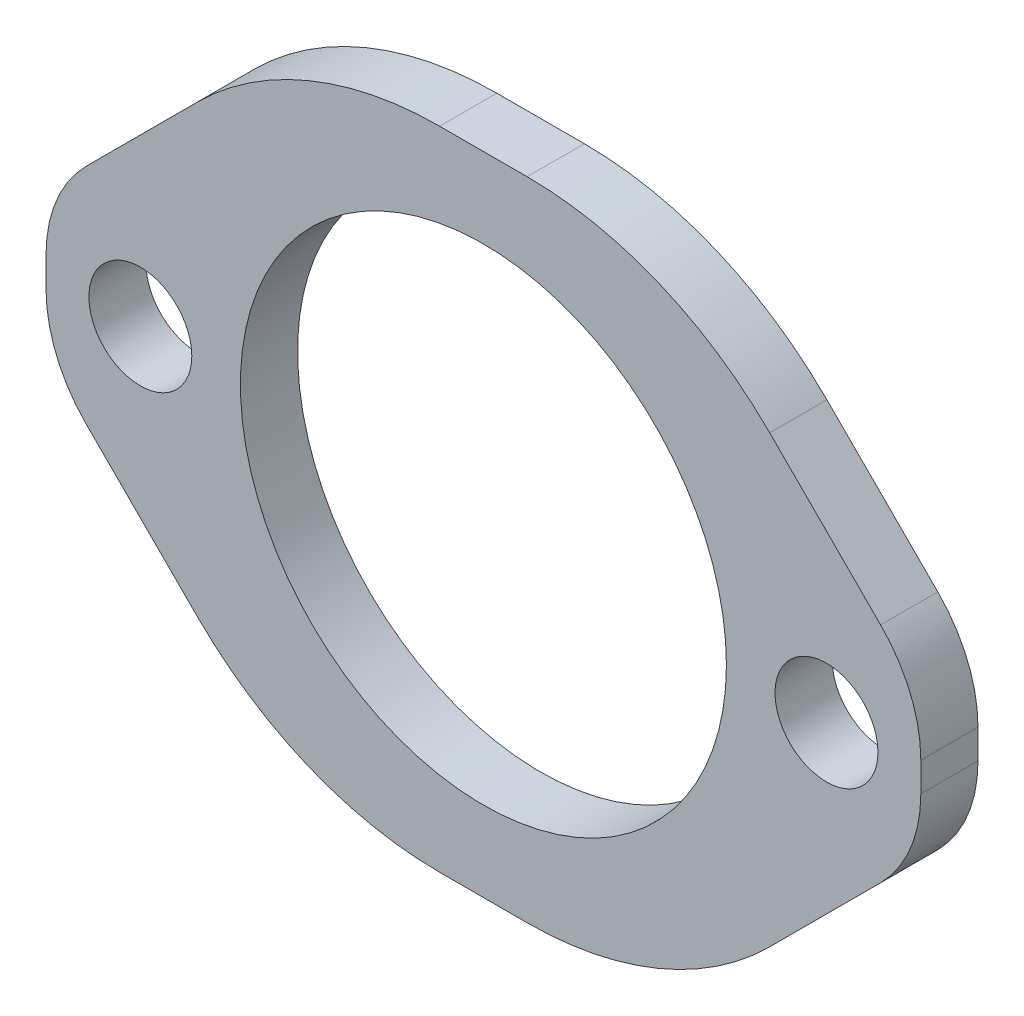
SolidWorks part; units mm, degrees
ref_plane "Plan de face" through (0, 0, 0) normal (0, 0, 1) x (1, 0, 0)
ref_plane "Plan de dessus" through (0, 0, 0) normal (0, 1, 0) x (1, 0, 0)
ref_plane "Plan de droite" through (0, 0, 0) normal (1, 0, 0) x (0, 0, -1)
sketch "Esquisse1" plane through (0, 0, 0) normal (0, 0, 1) x (1, 0, 0)
  line L1 (-38.25, -28.25) -> (38.25, -28.25)
  line L2 (-38.25, -28.25) -> (-38.25, 28.25)
  line L3 (-38.25, 28.25) -> (38.25, 28.25)
  line L4 (38.25, -28.25) -> (38.25, 28.25)
  line L5 (-38.25, -28.25) -> (38.25, 28.25) construction
  line L6 (-38.25, 28.25) -> (38.25, -28.25) construction
  circle A0 centre (0, 0) radius 21.25
  circle A1 centre (30, 0) radius 4.5
  circle A2 centre (-30, 0) radius 4.5
  dimension "D1" = 42.5
  dimension "D4" = 9
  dimension "D5" = 9
  dimension "D2" = 56.5
  dimension "D3" = 76.5
  dimension "D6" = 30
  dimension "D7" = 30
extrude "Boss.-Extru.1" add sketch "Esquisse1" along normal blind 5
chamfer "Chanfrein1" distance 22 angle 45 1 edges at (38.25, 28.25, 2.5)
chamfer "Chanfrein2" distance 22 angle 45 1 edges at (-38.25, 28.25, 2.5)
chamfer "Chanfrein3" distance 22 angle 45 1 edges at (-38.25, -28.25, 2.5)
chamfer "Chanfrein4" distance 22 angle 45 1 edges at (38.25, -28.25, 2.5)
fillet "Congé2" radius 30 1 edges at (16.25, 28.25, 2.5)
fillet "Congé3" radius 30 1 edges at (-16.25, 28.25, 2.5)
fillet "Congé4" radius 30 1 edges at (16.25, -28.25, 2.5)
fillet "Congé5" radius 30 1 edges at (-16.25, -28.25, 2.5)
fillet "Congé6" radius 12 1 edges at (38.25, 6.25, 2.5)
fillet "Congé7" radius 12 1 edges at (38.25, -6.25, 2.5)
fillet "Congé8" radius 12 1 edges at (-38.25, 6.25, 2.5)
fillet "Congé9" radius 12 1 edges at (-38.25, -6.25, 2.5)
